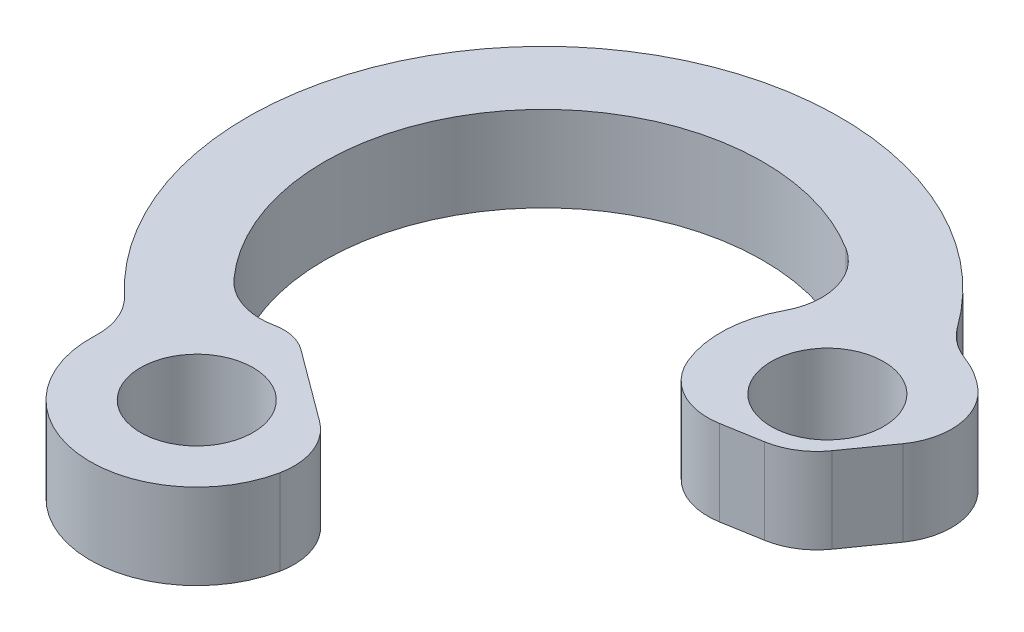
SolidWorks part; units mm, degrees
material "PLA"
ref_plane "Front Plane" through (0, 0, 0) normal (0, 0, 1) x (1, 0, 0)
ref_plane "Top Plane" through (0, 0, 0) normal (0, 1, 0) x (1, 0, 0)
ref_plane "Right Plane" through (0, 0, 0) normal (1, 0, 0) x (0, 0, -1)
ref_plane "Plane1" through (0, 4, 0) normal (0, 1, 0) x (1, 0, 0)
sketch "Sketch1" plane through (0, 4, 0) normal (0, 1, 0) x (1, 0, 0)
  line L0 (85.7355, 77.324) -> (87.5472, 77.6362)
  line L1 (89.4867, 78.8598) -> (90.8599, 80.8006)
  line L2 (76.2817, 68.0338) -> (72.9157, 70.5218)
  circle A0 centre (72.5387, 66.0204) radius 2.6375
  circle A1 centre (87.0735, 81.0463) radius 2.6375
  arc A2 (68.497, 71.804) -> (81.6322, 87.3691) centre (76.1332, 78.6848) cw
  arc A3 (81.6322, 87.3691) -> (82.6696, 83.4139) centre (80.0273, 84.8345) cw
  arc A4 (82.6696, 83.4139) -> (82.4547, 79.1316) centre (87.0735, 81.0463) ccw
  arc A5 (82.4547, 79.1316) -> (85.7355, 77.324) centre (85.226, 80.2804) ccw
  arc A6 (87.5472, 77.6362) -> (89.4867, 78.8598) centre (87.0377, 80.5926) ccw
  arc A7 (90.8599, 80.8006) -> (90.417, 84.764) centre (88.4109, 82.5334) ccw
  arc A8 (90.417, 84.764) -> (88.8113, 85.7346) centre (87.0735, 81.0463) ccw
  arc A9 (88.8113, 85.7346) -> (87.418, 86.7966) centre (89.854, 88.5476) cw
  arc A10 (87.418, 86.7966) -> (66.604, 68.5685) centre (76.1332, 78.6848) ccw
  arc A11 (66.604, 68.5685) -> (67.5438, 66.2481) centre (64.547, 66.3847) cw
  arc A12 (67.5438, 66.2481) -> (77.4381, 65.0228) centre (72.5387, 66.0204) ccw
  arc A13 (77.4381, 65.0228) -> (76.2817, 68.0338) centre (74.4984, 65.6213) ccw
  arc A14 (72.9157, 70.5218) -> (71.3264, 70.873) centre (71.7268, 68.9135) ccw
  arc A15 (71.3264, 70.873) -> (68.497, 71.804) centre (70.7257, 73.8122) cw
extrude "Boss-Extrude1" add sketch "Sketch1" against normal blind 4
